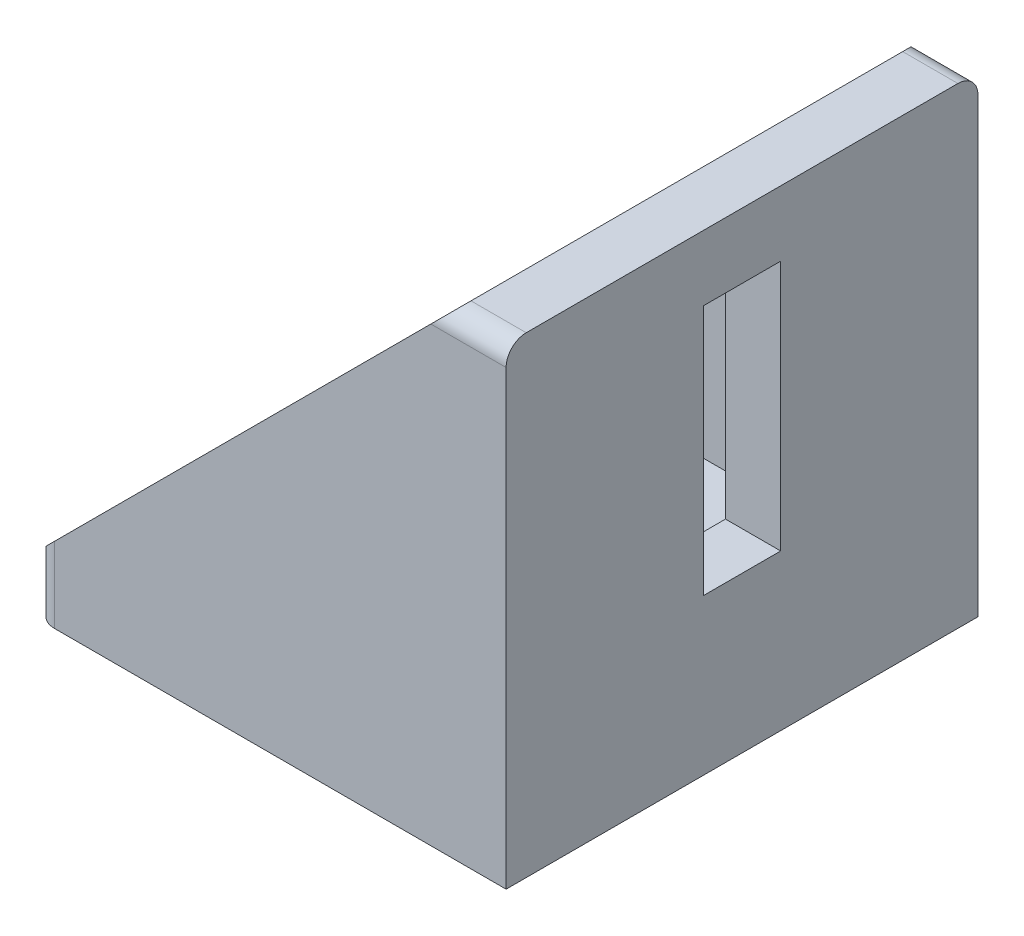
SolidWorks part; units mm, degrees
ref_plane "Front Plane" through (0, 0, 0) normal (0, 0, 1) x (1, 0, 0)
ref_plane "Top Plane" through (0, 0, 0) normal (0, 1, 0) x (1, 0, 0)
ref_plane "Right Plane" through (0, 0, 0) normal (1, 0, 0) x (0, 0, -1)
sketch "Sketch1" plane through (0, 0, 0) normal (0, 0, 1) x (1, 0, 0)
  line L0 (-47, 0) -> (0, 0)
  line L1 (0, 0) -> (0, 47)
  line L2 (0, 47) -> (-5.5, 47)
  line L3 (-5.5, 47) -> (-47, 5.5)
  line L4 (-47, 5.5) -> (-47, 0)
  point P6 (-47, 8.4177)
  dimension "D1" = 47
  dimension "D2" = 47
  dimension "D3" = 5.5
  dimension "D4" = 5.5
extrude "Boss-Extrude1" add sketch "Sketch1" along normal mid plane 47
sketch "Sketch2" plane through (0, 0, 0) normal (0, 0, 1) x (1, 0, 0)
  line L0 (-5.5, 47) -> (-5.5, 5.5)
  line L1 (-5.5, 5.5) -> (-47, 5.5)
  line L2 (-5.5, 47) -> (-47, 5.5)
extrude "Cut-Extrude1" cut sketch "Sketch2" against normal mid plane 36
sketch "Sketch3" plane through (-5.5, 0, 0) normal (-1, 0, 0) x (0, 0, 1)
  line L5 (-3.85, 15.5) -> (3.85, 15.5)
  line L6 (-3.85, 15.5) -> (-3.85, 40.5)
  line L11 (-3.85, 40.5) -> (3.85, 40.5)
  line L17 (3.85, 15.5) -> (3.85, 40.5)
  line L18 (-3.85, 15.5) -> (3.85, 40.5) construction
  line L23 (-3.85, 40.5) -> (3.85, 15.5) construction
  point P0 (0, 28)
  point P5 (0, 0)
  dimension "D1" = 25
  dimension "D2" = 7.7
  dimension "D3" = 28
extrude "Cut-Extrude2" cut sketch "Sketch3" against normal through all
sketch "Sketch4" plane through (0, 5.5, 0) normal (0, 1, 0) x (1, 0, 0)
  line L1 (-37.5, -3.85) -> (-12.5, -3.85)
  line L2 (-37.5, -3.85) -> (-37.5, 3.85)
  line L3 (-37.5, 3.85) -> (-12.5, 3.85)
  line L4 (-12.5, -3.85) -> (-12.5, 3.85)
  line L5 (-37.5, -3.85) -> (-12.5, 3.85) construction
  line L6 (-37.5, 3.85) -> (-12.5, -3.85) construction
  point P0 (-25, 0)
  point P5 (0, 0)
  dimension "D1" = 25
  dimension "D2" = 25
  dimension "D3" = 7.7
extrude "Cut-Extrude3" cut sketch "Sketch4" against normal through all
fillet "Fillet1" radius 2 4 edges at (-47, 2.75, -23.5) (-47, 2.75, 23.5) (-2.75, 47, -23.5) (-2.75, 47, 23.5)
